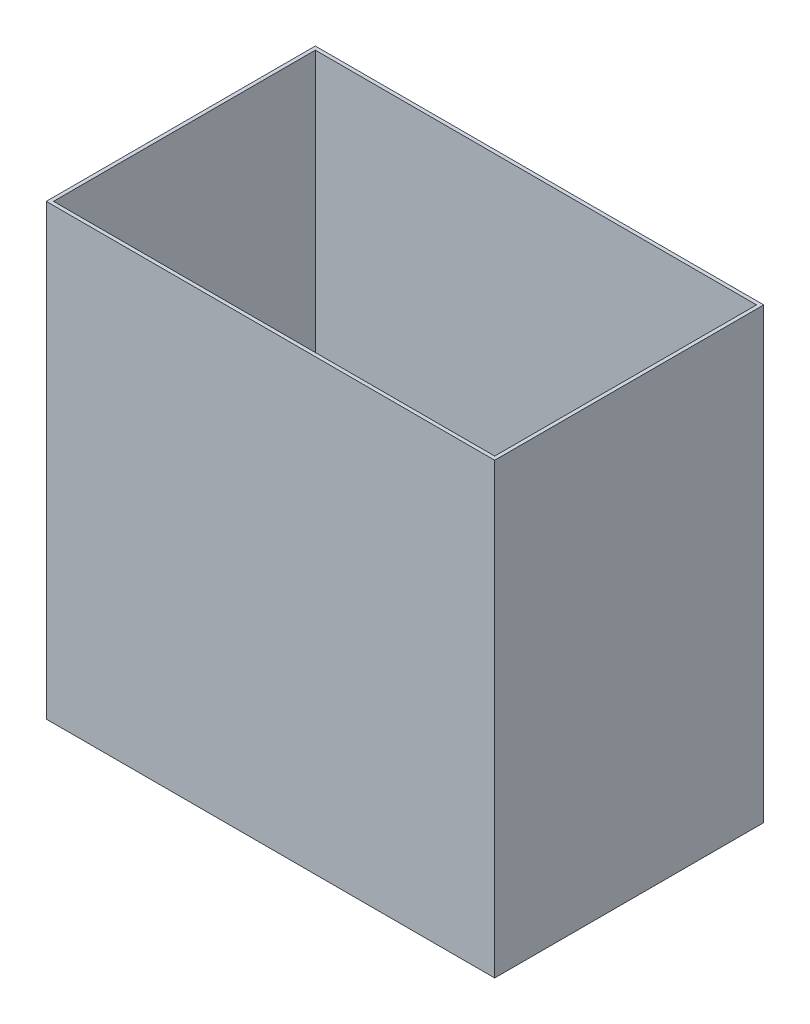
SolidWorks part; units mm, degrees
ref_plane "前视基准面" through (0, 0, 0) normal (0, 0, 1) x (1, 0, 0)
ref_plane "上视基准面" through (0, 0, 0) normal (0, 1, 0) x (1, 0, 0)
ref_plane "右视基准面" through (0, 0, 0) normal (1, 0, 0) x (0, 0, -1)
sketch "草图1" plane through (0, 0, 0) normal (0, 0, 1) x (1, 0, 0)
  line L13 (0, 0) -> (250, 0)
  line L14 (0, 0) -> (0, 250)
  line L15 (0, 250) -> (250, 250)
  line L16 (250, 0) -> (250, 250)
extrude "凸台-拉伸2" add sketch "草图1" along normal blind 150
sketch "草图3" plane through (0, 0, 0) normal (0, 1, 0) x (1, 0, 0)
  line L3 (2, -2) -> (2, -148)
  line L5 (248, -2) -> (248, -148)
  line L7 (248, -2) -> (2, -2)
  line L13 (2, -148) -> (248, -148)
extrude "切除-拉伸1" cut sketch "草图3" against normal blind 248 from surface at 250 starting at face at (125, 250, 75)
